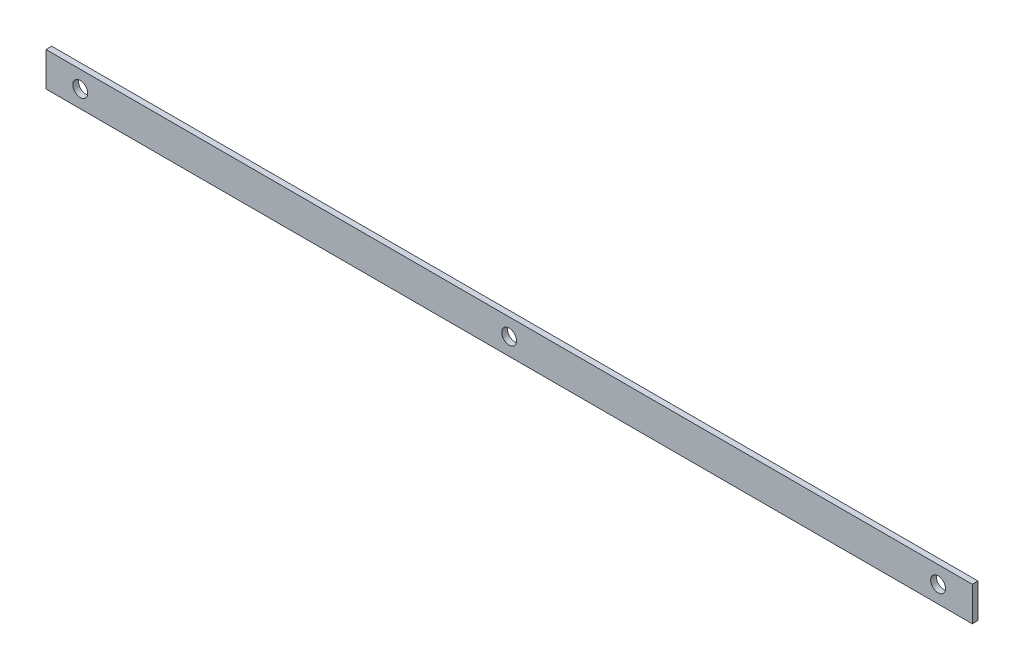
SolidWorks part; units mm, degrees
ref_plane "Plan de face" through (0, 0, 0) normal (0, 0, 1) x (1, 0, 0)
ref_plane "Plan de dessus" through (0, 0, 0) normal (0, 1, 0) x (1, 0, 0)
ref_plane "Plan de droite" through (0, 0, 0) normal (1, 0, 0) x (0, 0, -1)
sketch "Esquisse1" plane through (0, 0, 0) normal (0, 0, 1) x (1, 0, 0)
  line L0 (-406, 0) -> (406, 0)
other "Elément mécano-soudé1"
ref_plane "Plan1" through (-406, 0, 0) normal (1, 0, 0) x (0, 1, 0)
sketch "plat" plane through (-406, 0, 0) normal (1, 0, 0) x (0, 1, 0)
  line L0 (-15, 0) -> (15, 0) construction
  line L1 (-15, 2.5) -> (15, 2.5)
  line L2 (-15, 2.5) -> (-15, -2.5)
  line L3 (-15, -2.5) -> (15, -2.5)
  line L4 (15, 2.5) -> (15, -2.5)
  line L5 (0, 2.5) -> (0, -2.5) construction
  point P8 (0, 0)
  dimension "B" = 30
  dimension "A" = 5
sketch "Esquisse2" plane through (0, 0, -2.5) normal (0, 0, -1) x (-1, 0, 0)
  line L0 (406, 0) -> (-406, 0) construction
  line L1 (406, -15) -> (406, 15) construction
  line L2 (-406, -15) -> (-406, 15) construction
  point P0 (376, 0)
  point P5 (-376, 0)
ref_plane "Plan2" through (376, 0, 0) normal (1, 0, 0) x (0, 0, -1)
hole_wizard "Diamètre du perçage Ø13.0 (13)1" positions "Esquisse3" profile "Esquisse4" hole size "Ø13.0" standard "ISO" end condition through all
sketch "Esquisse3" plane through (0, 0, -2.5) normal (0, 0, -1) x (-1, 0, 0)
  point P0 (376, 0)
sketch "Esquisse4" plane through (-376, 0, -2.5) normal (1, 0, 0) x (0, 1, 0)
  line L0 (0, 0) -> (0, 5)
  line L1 (0, 5) -> (6.5, 5)
  line L2 (6.5, 5) -> (6.5, 0)
  line L5 (6.5, 0) -> (0, 0)
  line L11 (0, -6.35) -> (0, 107.95) construction
  dimension "Diamètre du perçage jusqu'au prochain" = 13
  dimension "Profondeur du perçage jusqu'au prochain" = 5
pattern_linear "Répétition linéaire2" count 3 spacing 376 along (1, 0, 0) of "Diamètre du perçage Ø13.0 (13)1"
equation "\"D2@Esquisse2\"=\"D1@Esquisse2\""
